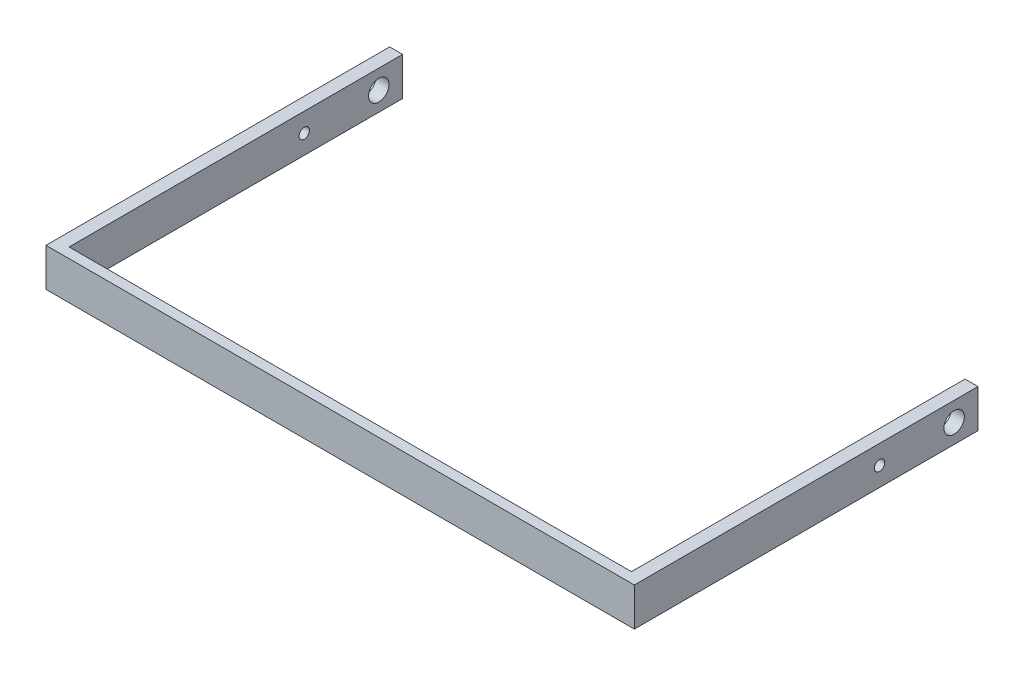
SolidWorks part; units mm, degrees
ref_plane "Front Plane" through (0, 0, 0) normal (0, 0, 1) x (1, 0, 0)
ref_plane "Top Plane" through (0, 0, 0) normal (0, 1, 0) x (1, 0, 0)
ref_plane "Right Plane" through (0, 0, 0) normal (1, 0, 0) x (0, 0, -1)
sketch "Sketch1" plane through (0, 0, 0) normal (-1, 0, 0) x (0, 0, 1)
  line L2 (132.6877, -32.3125) -> (308.8313, -32.3125)
  line L3 (132.6877, -32.3125) -> (132.6877, -52.5119)
  line L4 (132.6877, -52.5119) -> (308.8313, -52.5119)
  line L5 (308.8313, -32.3125) -> (308.8313, -52.5119)
  circle A2 centre (145.2964, -42.4122) radius 5.3975
  circle A3 centre (184.6659, -42.4122) radius 2.7392
  circle A4 centre (194.4098, -42.4122) radius 2.7392 construction
  point P0 (184.6659, -42.4122)
  point P12 (132.6877, -42.4122)
extrude "Boss-Extrude1" add sketch "Sketch1" along normal blind 6.858
sketch "Sketch5" plane through (0, 0, 308.8313) normal (0, 0, 1) x (1, 0, 0)
  line L0 (-6.858, -32.3125) -> (0, -32.3125) construction
  line L1 (-6.858, -52.5119) -> (303.8133, -52.5119)
  line L2 (-6.858, -52.5119) -> (-6.858, -32.3125)
  line L3 (-6.858, -32.3125) -> (303.8133, -32.3125)
  line L4 (303.8133, -52.5119) -> (303.8133, -32.3125)
  line L5 (148.4777, -32.3125) -> (148.4777, -52.5119) construction
extrude "Boss-Extrude4" add sketch "Sketch5" along normal blind 5.334
sketch "Sketch7" plane through (0, -32.3125, 0) normal (0, 1, 0) x (1, 0, 0)
  line L0 (148.4777, -308.8313) -> (148.4777, -314.1653) construction
  line L1 (-6.858, -308.8313) -> (303.8133, -308.8313) construction
  line L2 (303.8133, -314.1653) -> (-6.858, -314.1653) construction
ref_plane "Plane1" through (148.4777, 0, 0) normal (-1, 0, 0) x (0, 0, 1)
mirror "Mirror1" about plane through (148.4777, 0, 0) normal (-1, 0, 0) of "Boss-Extrude1"
